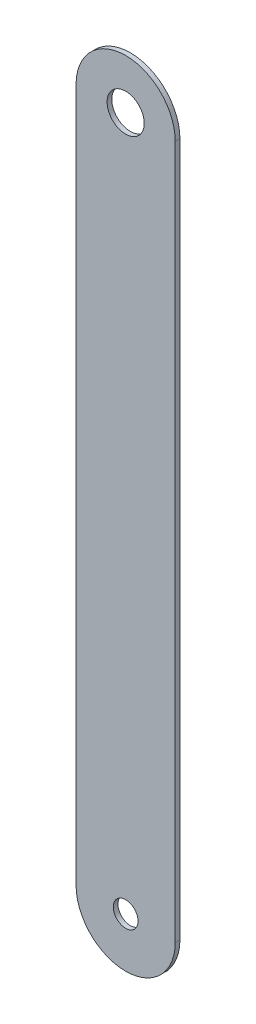
SolidWorks part; units mm, degrees
material "Alloy Steel"
ref_plane "Front" through (0, 0, 0) normal (0, 0, 1) x (1, 0, 0)
ref_plane "Top" through (0, 0, 0) normal (0, 1, 0) x (1, 0, 0)
ref_plane "Right" through (0, 0, 0) normal (1, 0, 0) x (0, 0, -1)
sketch "Sketch1" plane through (0, 0, 0) normal (0, 0, 1) x (1, 0, 0)
  line L1 (-12.7, 88.9) -> (12.7, 88.9)
  line L2 (-12.7, 88.9) -> (-12.7, -88.9)
  line L3 (-12.7, -88.9) -> (12.7, -88.9)
  line L4 (12.7, 88.9) -> (12.7, -88.9)
  line L5 (-12.7, 88.9) -> (12.7, -88.9) construction
  line L6 (-12.7, -88.9) -> (12.7, 88.9) construction
  arc A0 (-12.7, 88.9) -> (12.7, 88.9) centre (0, 88.9) cw
  arc A1 (-12.7, -88.9) -> (12.7, -88.9) centre (0, -88.9) ccw
  circle A2 centre (0, 88.9) radius 4.7625
  circle A3 centre (0, -88.9) radius 3.175
  point P0 (0, 0)
  dimension "D2" = 12.7
  dimension "D4" = 12.7
  dimension "D5" = 9.525
  dimension "D6" = 6.35
  dimension "D1" = 25.4
  dimension "D3" = 177.8
extrude "Boss-Extrude1" add sketch "Sketch1" along normal blind 1.2 contours A3 L3 L4 L1 A2 L2 | A2 L1 A0 | A3 L3 A1
